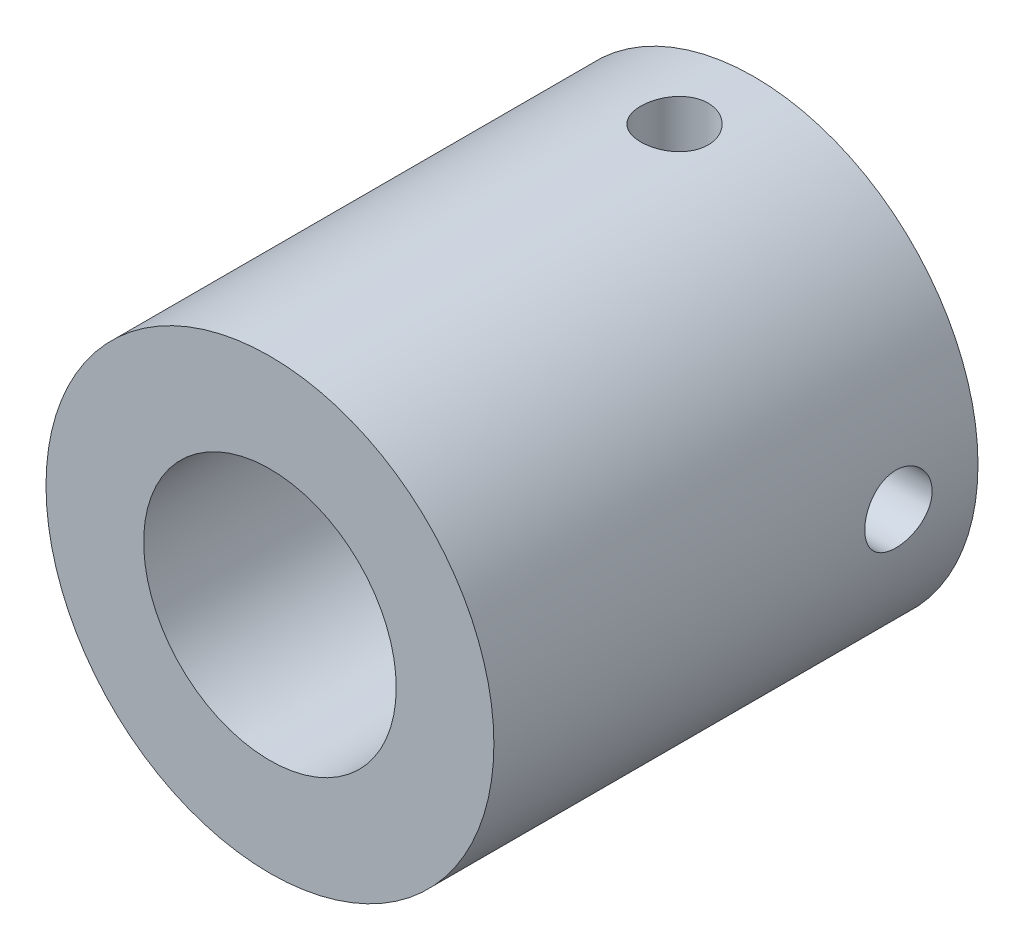
SolidWorks part; units mm, degrees
ref_plane "Front Plane" through (0, 0, 0) normal (0, 0, 1) x (1, 0, 0)
ref_plane "Top Plane" through (0, 0, 0) normal (0, 1, 0) x (1, 0, 0)
ref_plane "Right Plane" through (0, 0, 0) normal (1, 0, 0) x (0, 0, -1)
sketch "Sketch1" plane through (0, 0, 0) normal (0, 0, 1) x (1, 0, 0)
  circle A0 centre (0, 0) radius 16.891
  circle A1 centre (0, 0) radius 9.525
extrude "Boss-Extrude1" add sketch "Sketch1" along normal blind 36.5125
ref_plane "Plane1" through (16.891, 0, 0) normal (1, 0, 0) x (0, 0, -1)
sketch "Sketch2" plane through (16.891, 0, 0) normal (1, 0, 0) x (0, 0, -1)
  line L0 (0, 0) -> (-5.9995, 0) construction
  circle A0 centre (-5.9995, 0) radius 2.54
extrude "Cut-Extrude1" cut sketch "Sketch2" against normal blind 36.5125
pattern_circular "CirPattern1" count 4 over 360 about axis through (0, 0, 36.5125) along (0, 0, -1) of "Cut-Extrude1"
